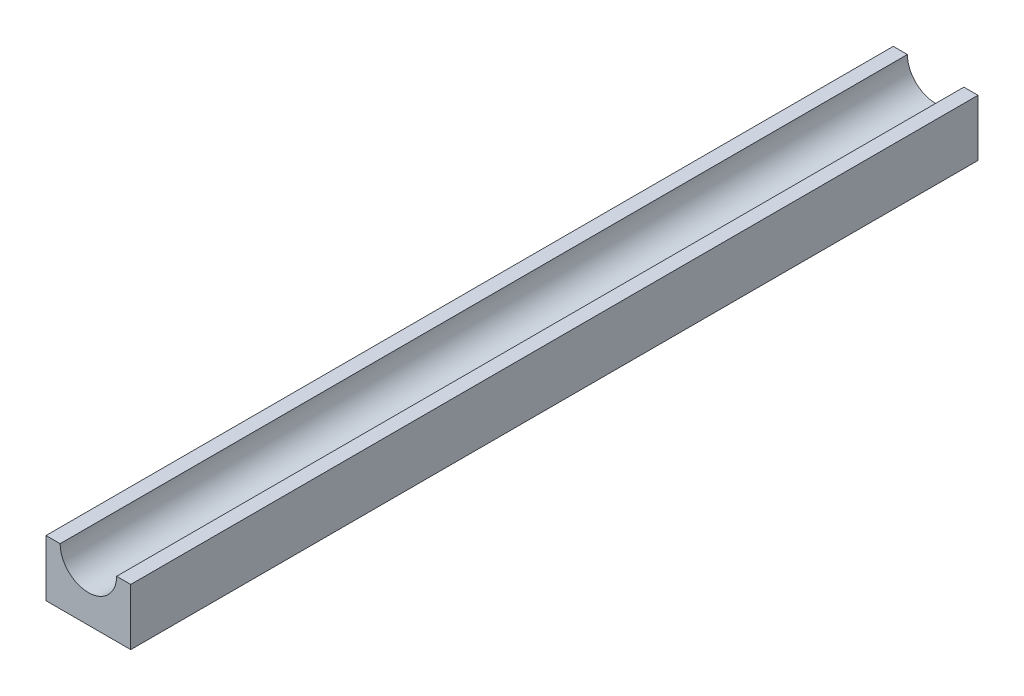
SolidWorks part; units mm, degrees
ref_plane "Front Plane" through (0, 0, 0) normal (0, 0, 1) x (1, 0, 0)
ref_plane "Top Plane" through (0, 0, 0) normal (0, 1, 0) x (1, 0, 0)
ref_plane "Right Plane" through (0, 0, 0) normal (1, 0, 0) x (0, 0, -1)
sketch "Sketch1" plane through (0, 0, 0) normal (0, 0, 1) x (1, 0, 0)
  line L1 (-7.5, 5) -> (7.5, 5)
  line L2 (-7.5, 5) -> (-7.5, -5)
  line L3 (-7.5, -5) -> (7.5, -5)
  line L4 (7.5, 5) -> (7.5, -5)
  line L5 (-7.5, 5) -> (7.5, -5) construction
  line L6 (-7.5, -5) -> (7.5, 5) construction
  circle A1 centre (0, 5) radius 5
  point P0 (0, 0)
  dimension "D3" = 10
  dimension "D1" = 10
  dimension "D2" = 15
extrude "Boss-Extrude1" add sketch "Sketch1" along normal blind 150
ref_plane "Plane1" through (0, 0, 15) normal (0, 0, -1) x (-1, 0, 0)
sketch "Sketch3" plane through (0, 0, 15) normal (0, 0, -1) x (-1, 0, 0)
  line L0 (7.5, -5) -> (-7.5, -5) construction
  line L1 (1.5, -5) -> (-1.5, -5)
  line L2 (1.5, -5) -> (1.5, -7)
  line L3 (1.5, -7) -> (-1.5, -7)
  line L4 (-1.5, -5) -> (-1.5, -7)
  line L5 (1.5, -5) -> (-1.5, -7) construction
  line L6 (1.5, -7) -> (-1.5, -5) construction
  arc A0 (-1.5, -7) -> (1.5, -7) centre (0, -7) ccw
  circle A1 centre (0, -7) radius 0.5
  point P0 (0, -6)
  point P7 (0, -5)
  point P8 (0, -5)
  dimension "D3" = 1
  dimension "D1" = 2
  dimension "D2" = 3
ref_plane "Plane2" through (0, 0, 82.5) normal (0, 0, 1) x (1, 0, 0)
ref_plane "Plane3" through (0, 0, 0) normal (-1, 0, 0) x (0, 0, 1)
sketch "Sketch6" plane through (0, 0, 0) normal (-1, 0, 0) x (0, 0, 1)
  line L0 (150, -5) -> (0, -5) construction
  line L1 (72.5, -5) -> (77.5, -5)
  line L2 (72.5, -5) -> (72.5, -8)
  line L3 (72.5, -8) -> (77.5, -8)
  line L4 (77.5, -5) -> (77.5, -8)
  line L5 (72.5, -5) -> (77.5, -8) construction
  line L6 (72.5, -8) -> (77.5, -5) construction
  line L7 (150, -5) -> (0, -5)
  line L8 (150, 5) -> (150, -5) construction
  circle A0 centre (75, -8) radius 2.5
  point P0 (75, -6.5)
  dimension "D1" = 5
  dimension "D2" = 75
  dimension "D3" = 3
extrude "Boss-Extrude6" add sketch "Sketch6" along normal mid plane 3 contours L3 A0 | L3 A0 | A0 L4 L1 L2
sketch "Sketch7" plane through (0, 0, 0) normal (-1, 0, 0) x (0, 0, 1)
  arc A0 (72.5, -8) -> (77.5, -8) centre (75, -8) ccw construction
  arc A1 (72.5, -8) -> (77.5, -8) centre (75, -8) ccw
  circle A2 centre (75, -8) radius 0.5
  dimension "D1" = 1
extrude "Boss-Extrude7" add sketch "Sketch7" along normal mid plane 8 contours A2
ref_plane "Plane4" through (0, 0, 45) normal (0, 0, -1) x (-1, 0, 0)
mirror "Mirror1" about plane through (0, 0, 45) normal (0, 0, -1) of "Boss-Extrude6"
mirror "Mirror2" about plane through (0, 0, 45) normal (0, 0, -1) of "Boss-Extrude7"
